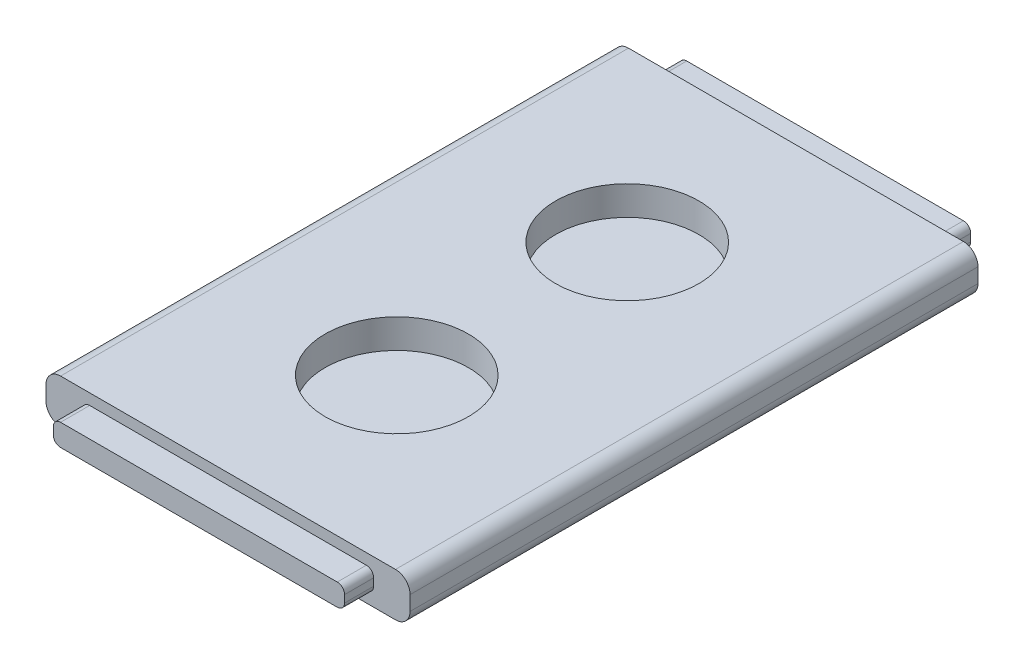
SolidWorks part; units mm, degrees
ref_plane "Front Plane" through (0, 0, 0) normal (0, 0, 1) x (1, 0, 0)
ref_plane "Top Plane" through (0, 0, 0) normal (0, 1, 0) x (1, 0, 0)
ref_plane "Right Plane" through (0, 0, 0) normal (1, 0, 0) x (0, 0, -1)
sketch "Sketch1" plane through (0, 0, 0) normal (0, 1, 0) x (1, 0, 0)
  line L1 (-31.75, 49.53) -> (31.75, 49.53)
  line L2 (-31.75, 49.53) -> (-31.75, -49.53)
  line L3 (-31.75, -49.53) -> (31.75, -49.53)
  line L4 (31.75, 49.53) -> (31.75, -49.53)
  line L5 (-31.75, 49.53) -> (31.75, -49.53) construction
  line L6 (-31.75, -49.53) -> (31.75, 49.53) construction
  point P0 (0, 0)
  dimension "D1" = 63.5
  dimension "D2" = 99.06
extrude "Boss-Extrude1" add sketch "Sketch1" along normal blind 7.62
sketch "Sketch2" plane through (0, 7.62, 0) normal (0, 1, 0) x (1, 0, 0)
  circle A1 centre (0, -20.1) radius 12.5
  circle A2 centre (0, 20.1) radius 12.5
  dimension "D2" = 25
  dimension "D3" = 25
extrude "Cut-Extrude1" cut sketch "Sketch2" against normal blind 5.08
sketch "Sketch3" plane through (0, 0, 49.53) normal (0, 0, 1) x (1, 0, 0)
  line L6 (-25.4, 1.905) -> (25.4, 1.905)
  line L7 (-25.4, 1.905) -> (-25.4, 5.715)
  line L8 (-25.4, 5.715) -> (25.4, 5.715)
  line L9 (25.4, 1.905) -> (25.4, 5.715)
  line L10 (-25.4, 1.905) -> (25.4, 5.715) construction
  line L11 (-25.4, 5.715) -> (25.4, 1.905) construction
  point P7 (0, 3.81)
  dimension "D2" = 50.8
fillet "Fillet1" radius 2.54 4 edges at (-31.75, 7.62, 0) (31.75, 7.62, 0) (31.75, 0, 0) (-31.75, 0, 0)
sketch "Sketch4" plane through (0, 0, -49.53) normal (0, 0, -1) x (-1, 0, 0)
  line L3 (-25.4, 1.8671) -> (25.4, 1.8671)
  line L4 (-25.4, 1.8671) -> (-25.4, 5.6771)
  line L5 (-25.4, 5.6771) -> (25.4, 5.6771)
  line L6 (25.4, 1.8671) -> (25.4, 5.6771)
  line L7 (-25.4, 1.8671) -> (25.4, 5.6771) construction
  line L8 (-25.4, 5.6771) -> (25.4, 1.8671) construction
  dimension "D1" = 3.81
  dimension "2" = 50.8
sketch "Sketch6" plane through (0, 2.54, 0) normal (0, 1, 0) x (1, 0, 0)
extrude "Boss-Extrude2" add sketch "Sketch3" along normal blind 5.08 contours L8 L9 L6 L7
fillet "Fillet2" radius 1.27 4 edges at (-25.4, 1.905, 52.07) (-25.4, 5.715, 52.07) (25.4, 5.715, 52.07) (25.4, 1.905, 52.07)
extrude "Boss-Extrude3" add sketch "Sketch4" along normal blind 5.08
fillet "Fillet3" radius 1.27 4 edges at (-25.4, 1.8671, -52.07) (-25.4, 5.6771, -52.07) (25.4, 1.8671, -52.07) (25.4, 5.6771, -52.07)
